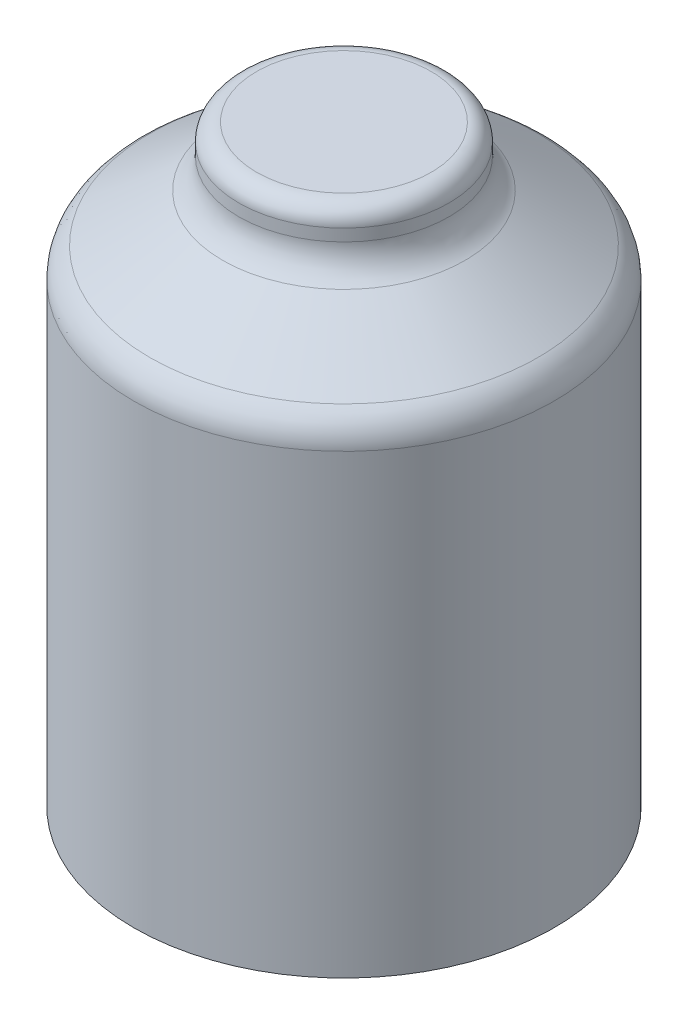
SolidWorks part; units mm, degrees
ref_plane "Front Plane" through (0, 0, 0) normal (0, 0, 1) x (1, 0, 0)
ref_plane "Top Plane" through (0, 0, 0) normal (0, 1, 0) x (1, 0, 0)
ref_plane "Right Plane" through (0, 0, 0) normal (1, 0, 0) x (0, 0, -1)
sketch "Sketch1" plane through (0, 0, 0) normal (0, 0, 1) x (1, 0, 0)
  line L0 (0, 0) -> (0, -33.4204)
  line L5 (0, -33.4204) -> (11.8467, -33.4204)
  line L6 (11.8467, -33.4204) -> (11.8467, -7.7087)
  line L7 (10.9403, -6.0342) -> (6.8298, -3.3499)
  line L8 (5.9234, -1.6753) -> (5.9234, -1)
  line L9 (4.9234, 0) -> (0, 0)
  arc A0 (11.8467, -7.7087) -> (10.9403, -6.0342) centre (9.8467, -7.7087) ccw
  arc A1 (6.8298, -3.3499) -> (5.9234, -1.6753) centre (7.9234, -1.6753) cw
  arc A2 (5.9234, -1) -> (4.9234, 0) centre (4.9234, -1) ccw
  point P4 (0, 0)
  dimension "D1" = 2
  dimension "D2" = 2
  dimension "D3" = 1
revolve "Revolve1" add sketch "Sketch1" angle 360 about L0
equation "\"gv\" = 6"
